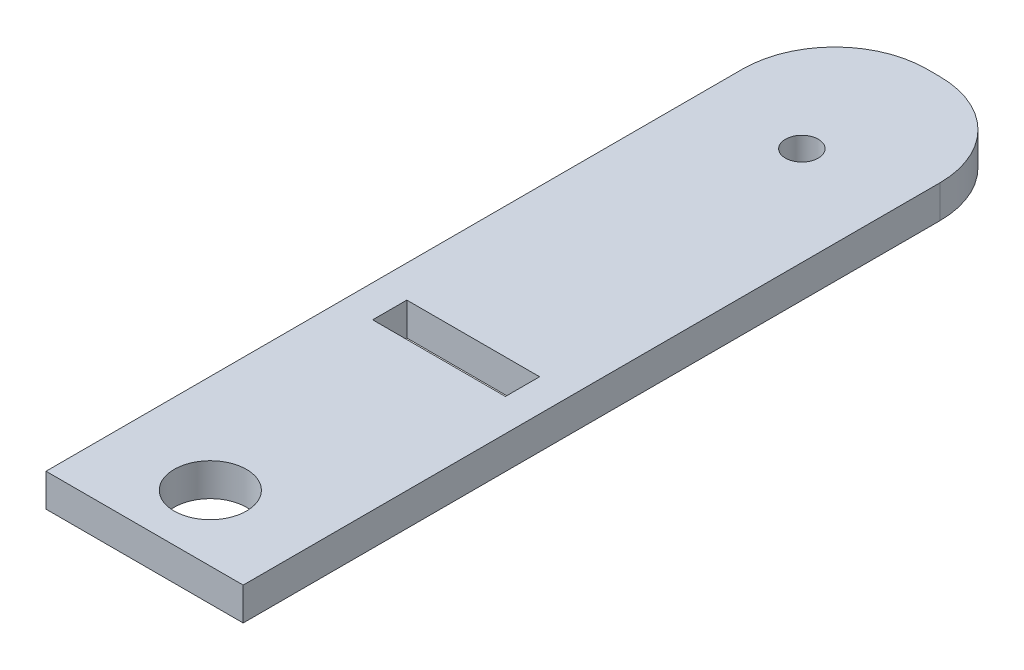
SolidWorks part; units mm, degrees
ref_plane "Front Plane" through (0, 0, 0) normal (0, 0, 1) x (1, 0, 0)
ref_plane "Top Plane" through (0, 0, 0) normal (0, 1, 0) x (1, 0, 0)
ref_plane "Right Plane" through (0, 0, 0) normal (1, 0, 0) x (0, 0, -1)
sketch "Sketch1" plane through (0, 0, 0) normal (0, 1, 0) x (1, 0, 0)
  line L1 (-9.525, 38.1) -> (9.525, 38.1)
  line L2 (-9.525, 38.1) -> (-9.525, -38.1)
  line L3 (-9.525, -38.1) -> (9.525, -38.1)
  line L4 (9.525, 38.1) -> (9.525, -38.1)
  line L5 (-6.4135, -6.35) -> (6.4135, -6.35)
  line L6 (-6.4135, -6.35) -> (-6.4135, -9.652)
  line L7 (-6.4135, -9.652) -> (6.4135, -9.652)
  line L8 (6.4135, -6.35) -> (6.4135, -9.652)
  circle A0 centre (0, 25.4) radius 1.5875
  circle A1 centre (0, -31.75) radius 3.4925
  point P8 (0, 38.1)
  point P10 (9.525, 0)
  point P11 (0, -38.1)
  point P16 (0, -6.35)
  dimension "D3" = 3.175
  dimension "D4" = 6.985
  dimension "D1" = 19.05
  dimension "D2" = 76.2
  dimension "D5" = 12.7
  dimension "D6" = 6.35
  dimension "D7" = 3.302
  dimension "D8" = 12.827
  dimension "D9" = 6.35
extrude "Boss-Extrude1" add sketch "Sketch1" along normal blind 3.175
fillet "Fillet1" radius 8.89 1 edges at (9.525, 1.5875, -38.1)
fillet "Fillet2" radius 8.89 1 edges at (-9.525, 1.5875, -38.1)
